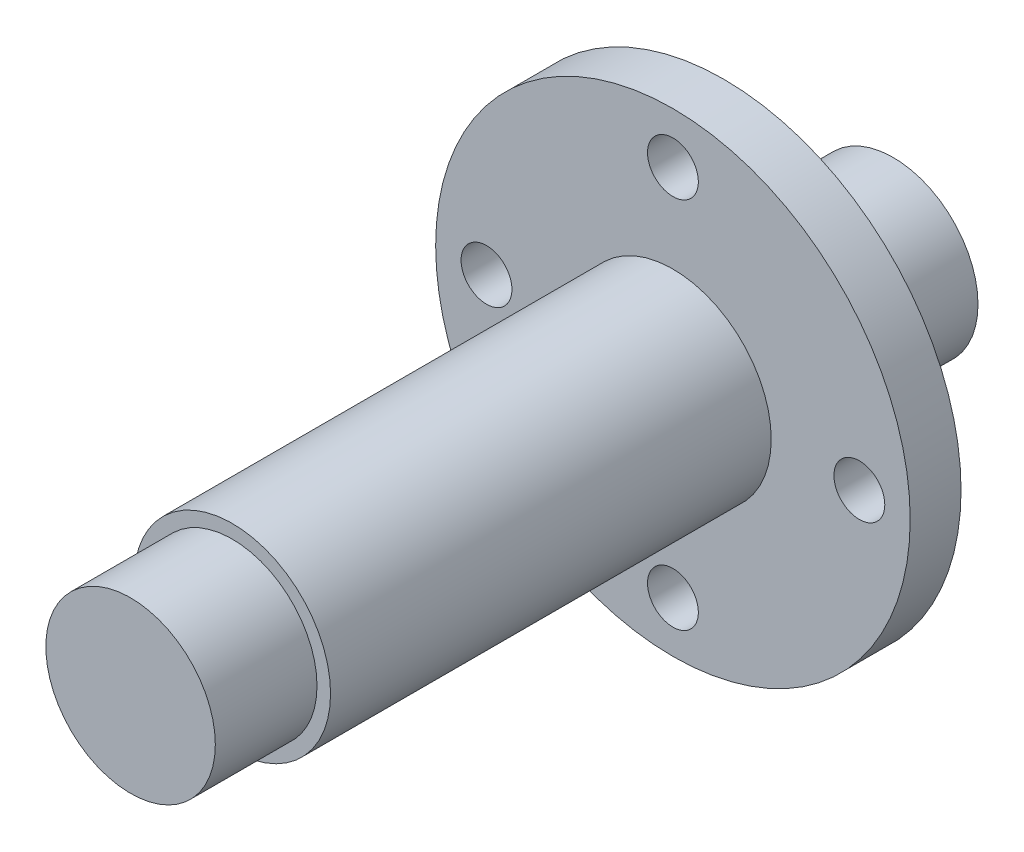
SolidWorks part; units mm, degrees
ref_plane "Alzado" through (0, 0, 0) normal (0, 0, 1) x (1, 0, 0)
ref_plane "Planta" through (0, 0, 0) normal (0, 1, 0) x (1, 0, 0)
ref_plane "Vista lateral" through (0, 0, 0) normal (1, 0, 0) x (0, 0, -1)
sketch "Croquis1" plane through (0, 0, 0) normal (0, 0, 1) x (1, 0, 0)
  circle A0 centre (0, 0) radius 5
  dimension "D1" = 10
extrude "Saliente-Extruir1" add sketch "Croquis1" along normal blind 6
sketch "Croquis2" plane through (0, 0, 6) normal (0, 0, 1) x (1, 0, 0)
  circle A0 centre (0, 0) radius 5.8
  dimension "D1" = 11.6
extrude "Saliente-Extruir2" add sketch "Croquis2" along normal blind 4
sketch "Croquis3" plane through (0, 0, 10) normal (0, 0, 1) x (1, 0, 0)
  circle A0 centre (0, 0) radius 14
  dimension "D1" = 28
extrude "Saliente-Extruir3" add sketch "Croquis3" along normal blind 3
sketch "Croquis4" plane through (0, 0, 13) normal (0, 0, 1) x (1, 0, 0)
  circle A0 centre (0, 0) radius 5.8
  dimension "D1" = 11.6
extrude "Saliente-Extruir4" add sketch "Croquis4" along normal blind 26
sketch "Croquis5" plane through (0, 0, 39) normal (0, 0, 1) x (1, 0, 0)
  circle A0 centre (0, 0) radius 5
  dimension "D1" = 10
extrude "Saliente-Extruir5" add sketch "Croquis5" along normal blind 6
sketch "Croquis6" plane through (0, 0, 10) normal (0, 0, -1) x (-1, 0, 0)
  line L0 (0, 0) -> (11, 0) construction
  circle A0 centre (11, 0) radius 1.5
  circle A1 centre (0, -11) radius 1.5
  circle A2 centre (-11, 0) radius 1.5
  circle A3 centre (0, 11) radius 1.5
  point P13 (0, 0)
  dimension "D1" = 3
  dimension "D2" = 11
  dimension "D3" = 4
extrude "Cortar-Extruir1" cut sketch "Croquis6" against normal blind 6
